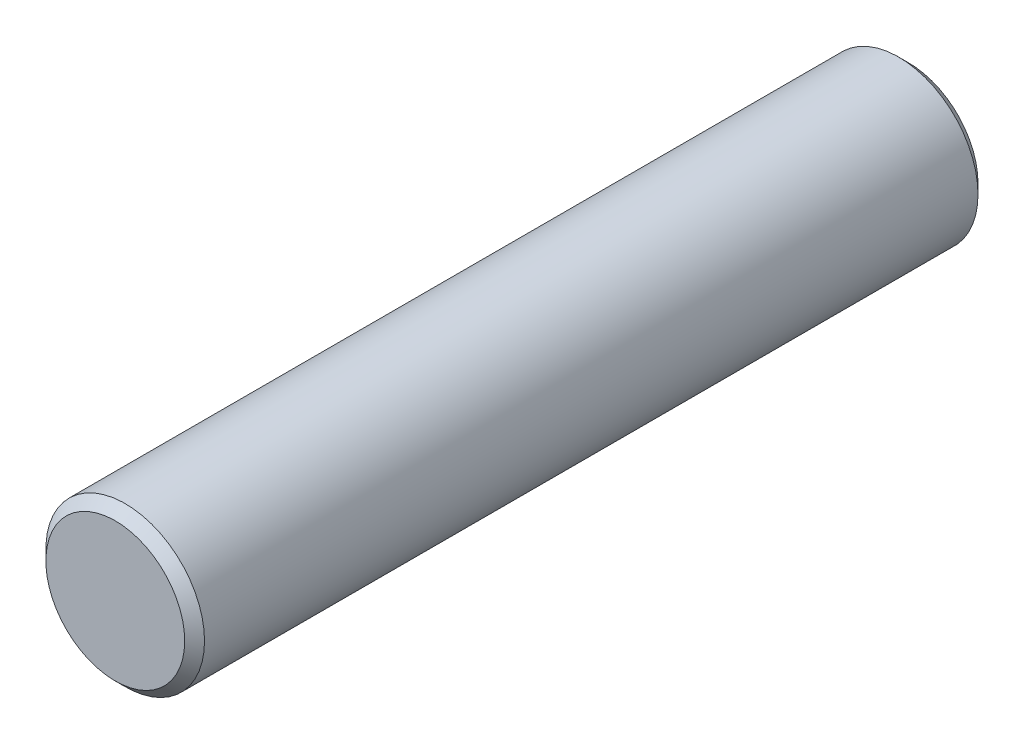
SolidWorks part; units mm, degrees
ref_plane "Alzado" through (0, 0, 0) normal (0, 0, 1) x (1, 0, 0)
ref_plane "Planta" through (0, 0, 0) normal (0, 1, 0) x (1, 0, 0)
ref_plane "Vista lateral" through (0, 0, 0) normal (1, 0, 0) x (0, 0, -1)
sketch "Croquis1" plane through (0, 0, 0) normal (0, 0, 1) x (1, 0, 0)
  circle A0 centre (0, 0) radius 4
  dimension "D1" = 8
extrude "Saliente-Extruir1" add sketch "Croquis1" along normal mid plane 40
chamfer "Chaflán1" distance 0.5 angle 45 2 edges at (4, 0, 20) (4, 0, -20)
